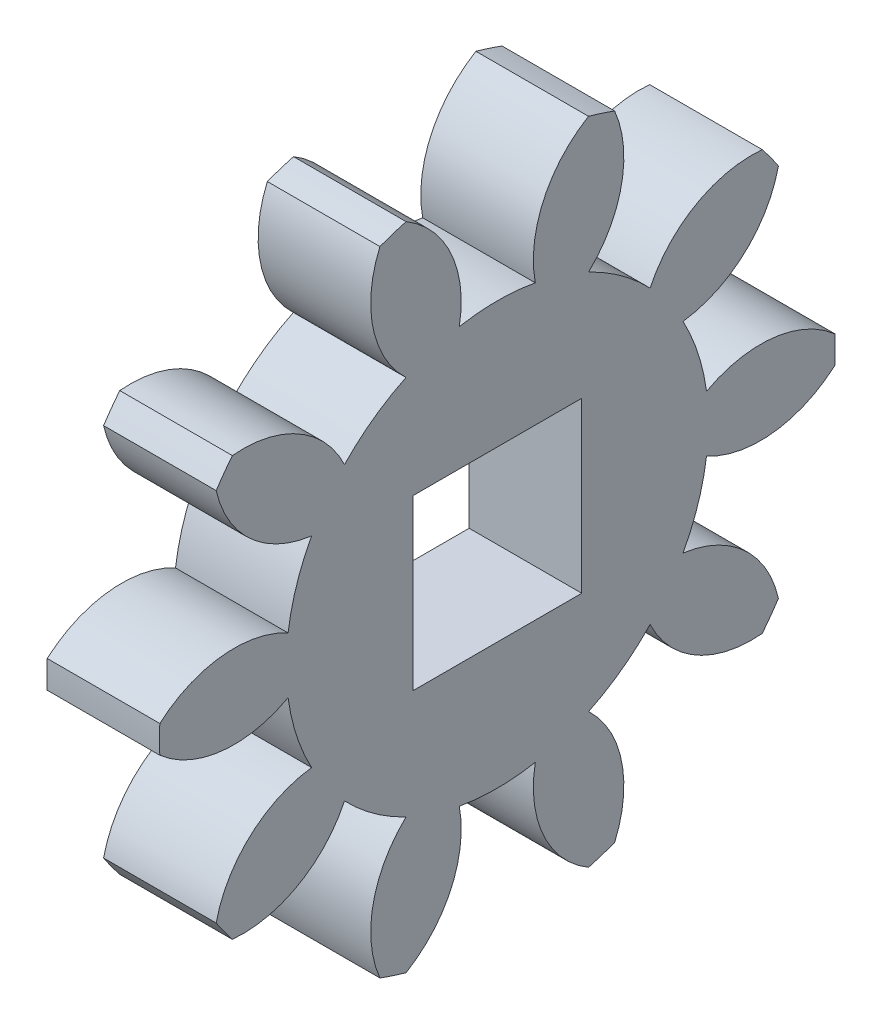
SolidWorks part; units mm, degrees
ref_plane "Plane1" through (0, 0, 0) normal (0, 0, 1) x (1, 0, 0)
ref_plane "Plane2" through (0, 0, 0) normal (0, 1, 0) x (1, 0, 0)
ref_plane "Plane3" through (0, 0, 0) normal (1, 0, 0) x (0, 0, -1)
other "Configuration Table"
sketch "HoldingSke" plane through (0, 0, 0) normal (0, 1, 0) x (1, 0, 0)
  line L0 (0, 0) -> (0.4924, -0.0868)
  line L1 (-15, 0) -> (100, 0) construction
  line L2 (0, 0) -> (-2.1039, 2.3779)
  line L3 (0, 0) -> (-11.863, 4.5341)
  line L4 (0, 0) -> (8.5048, 1.4996)
  line L5 (0, 0) -> (-46.8476, -17.4728)
  line L6 (0, 0) -> (-3.3159, -2.2372)
  line L7 (-2.1039, 2.3779) -> (8.6586, 51.2059)
  line L8 (-76.2, 54.61) -> (-75.9, 54.61)
  line L9 (-67.7845, 28.3722) -> (-49.3413, 33.142)
  line L10 (-76.2, 71.12) -> (104.1128, 71.12)
  line L11 (0, 0) -> (-4, 0)
  line L12 (-76.2, 101.6) -> (-76.133, 101.6)
  line L13 (24.9733, 27.94) -> (52.9518, 28.4284)
  line L14 (24.9733, 27.94) -> (24.9743, 27.94)
  line L15 (24.9733, 27.94) -> (100.4006, 29.5858)
  line L16 (-63.627, -2) -> (-12.827, -2)
  circle A0 centre (0, 0) radius 1
  circle A1 centre (0, 0) radius 7.499
  circle A2 centre (0, 0) radius 37.5
  circle A3 centre (0, 0) radius 1
  dimension "MHD" = 14.998
  dimension "Hub_dia" = 75
  dimension "Bore" = 2
  dimension "MBD" = 2
  dimension "Num_teeth" = 10
  dimension "Pitch" = 0.5
  dimension "Overall_len" = 50
  dimension "Show_teeth" = 10
  dimension "Thickness" = 4
  dimension "OAL" = 50.0001
  dimension "T_dim" = 0.3
  dimension "Ap" = 14.5
  dimension "H" = 19.05
  dimension "Pitch_radius" = 180.3128
  dimension "Width" = 4
  dimension "Backlash" = 0.067
  dimension "Addendum_fac" = 1
  dimension "Dedendum_fac" = 1.25
  dimension "Clearance_fac" = 0.25
  dimension "Dedendum_add" = 0.001
  dimension "Module" = 2
sketch "BasProSke" plane through (0, 0, 0) normal (0, 1, 0) x (1, 0, 0)
  line L0 (-10, 0) -> (60, 0) construction
  line L1 (0, 0) -> (0, 12)
  line L2 (0, 0) -> (4, 0)
  line L3 (4, 0) -> (4, 12)
  line L4 (4, 12) -> (0, 12)
  dimension "Thickness" = 4
  dimension "Diameter" = 24
revolve "Base-Revolve" add sketch "BasProSke" angle 360 about L0
sketch "TooCutSke" plane through (0, 0, 0) normal (1, 0, 0) x (0, 0, -1)
  line L1 (0, 0) -> (0, 107) construction
  line L2 (0, 0) -> (-1.6814, 9.8576) construction
  line L3 (0, 0) -> (-6.1153, 18.8209) construction
  line L4 (-1.6814, 9.8576) -> (-3.0576, 9.4105) construction
  arc A0 (1.35, 7.3765) -> (-1.35, 7.3765) centre (0, 0) ccw
  arc A1 (3.2708, 11.572) -> (-3.2708, 11.572) centre (0, 0) ccw
  circle A2 centre (0, 0) radius 10 construction
  circle A3 centre (0, 0) radius 9.6815 construction
  arc A4 (-1.35, 7.3765) -> (-3.2708, 11.572) centre (-5.2814, 8.1141) ccw
  arc A5 (3.2708, 11.572) -> (1.35, 7.3765) centre (5.2814, 8.1141) ccw
  dimension "Root_dia" = 14.998
  dimension "Overcut_dia" = 24.0508
  dimension "Pitch_dia" = 20
  dimension "Base_dia" = 19.363
  dimension "Flank_rad" = 4
  dimension "Half_ang" = 18
  dimension "Half_CT" = 1.4471
extrude "ToothCut" cut sketch "TooCutSke" along normal through all
fillet "Breaks" [suppressed] radius 0.04
fillet "RootFillets" [suppressed] radius 0.501
pattern_circular "TeethCuts" count 10 every 36 about axis through (-10, 0, 0) along (1, 0, 0) of "ToothCut", "RootFillets", "Breaks"
sketch "HubNeaOneSke" plane through (0, 0, 0) normal (-1, 0, 0) x (0, 0, 1)
  circle A0 centre (0, 0) radius 7.499
  dimension "Diameter" = 14.998
extrude "HubNearOne" [suppressed] add sketch "HubNeaOneSke" along normal blind 46.0001
sketch "HubNeaBotSke" plane through (0, 0, 0) normal (-1, 0, 0) x (0, 0, 1)
  circle A0 centre (0, 0) radius 7.499
  dimension "Diameter" = 14.998
extrude "HubNearBoth" [suppressed] add sketch "HubNeaBotSke" along normal blind 23
ref_plane "FarPln" through (4, 0, 0) normal (1, 0, 0) x (0, 0, -1)
sketch "HubFarSke" plane through (4, 0, 0) normal (1, 0, 0) x (0, 0, -1)
  circle A0 centre (0, 0) radius 7.499
  dimension "Diameter" = 14.998
extrude "HubFar" [suppressed] add sketch "HubFarSke" along normal blind 23
sketch "BorSke" plane through (0, 0, 0) normal (1, 0, 0) x (0, 0, -1)
  circle A0 centre (0, 0) radius 1
  dimension "Diameter" = 2
extrude "Bore" cut sketch "BorSke" along normal mid plane 100.0001
sketch "KeySke" plane through (0, 0, 0) normal (1, 0, 0) x (0, 0, -1)
  line L0 (-0.4, 0) -> (-0.4, 1.3)
  line L1 (-0.4, 1.3) -> (0.4, 1.3)
  line L2 (0.4, 1.3) -> (0.4, 0)
  line L3 (0, 0) -> (0, 34) construction
  line L4 (-0.4, 0) -> (0.4, 0)
  dimension "Offset" = 1.3
  dimension "Width" = 0.8
extrude "Keyway" [suppressed] cut sketch "KeySke" along normal mid plane 100.0001
pattern_circular "Keyway2" [suppressed] count 2 every 90 about axis through (-10, 0, 0) along (1, 0, 0)
sketch "草图1" plane through (0, 0, 0) normal (-1, 0, 0) x (0, 0, 1)
  line L1 (-3, 3) -> (3, 3)
  line L2 (-3, 3) -> (-3, -3)
  line L3 (-3, -3) -> (3, -3)
  line L4 (3, 3) -> (3, -3)
  line L5 (-3, 3) -> (3, -3) construction
  line L6 (-3, -3) -> (3, 3) construction
  point P0 (0, 0)
  dimension "D1" = 6
  dimension "D2" = 6
extrude "切除-拉伸2" cut sketch "草图1" against normal through all
equation "' \"Module@HoldingSke\" = 6.35"
equation "' \"Num_teeth@HoldingSke\" = 12"
equation "' \"Ap@HoldingSke\" =  20"
equation "' \"Ap@HoldingSke\" = 20"
equation "' \"Width@HoldingSke\" = 0.5 * 25.4"
equation "' \"Hub_dia@HoldingSke\"= 1 * 25.4"
equation "' \"Hub_dia@HoldingSke\" = 1 * 25.4"
equation "' \"Overall_len@HoldingSke\" = 1.0 * 25.4"
equation "' \"Bore@HoldingSke\" = 0.75 * 25.4"
equation "' \"T_dim@HoldingSke\" = 0.1 * 25.4"
equation "' \"Width@KeySke\" = 0.25 * 25.4"
equation "' \"Show_teeth@HoldingSke\" = 13"
equation "' \"Backlash@HoldingSke\" = 0.009 * 25.4"
equation "' \"Addendum_fac@HoldingSke\" = 1.0"
equation "' \"Dedendum_fac@HoldingSke\" = 1.25"
equation "' \"Dedendum_add@HoldingSke\" = 0.00005 * 25.4"
equation "' \"Clearance_fac@HoldingSke\" = 0.25"
equation "\"Pitch@HoldingSke\" = 1 / \"Module@HoldingSke\""
equation "\"Overcut_dia@TooCutSke\" = (\"Num_teeth@HoldingSke\" + 2 * \"Addendum_fac@HoldingSke\") / \"Pitch@HoldingSke\" + 0.002 * 25.4"
equation "\"Pitch_dia@TooCutSke\" = \"Num_teeth@HoldingSke\" / \"Pitch@HoldingSke\""
equation "\"Base_dia@TooCutSke\" = \"Num_teeth@HoldingSke\" / \"Pitch@HoldingSke\" * cos((\"Ap@HoldingSke\"  * 3.14159265 / 180))"
equation "\"Root_dia@TooCutSke\" = (\"Num_teeth@HoldingSke\" + 2) / \"Pitch@HoldingSke\" - 2 * (\"Addendum_fac@HoldingSke\" + \"Dedendum_fac@HoldingSke\") / \"Pitch@HoldingSke\" - \"Dedendum_add@HoldingSke\" * 2"
equation "\"Half_ang@TooCutSke\" = 180 / \"Num_teeth@HoldingSke\""
equation "\"Half_CT@TooCutSke\" = \"Num_teeth@HoldingSke\" / \"Pitch@HoldingSke\" * sin((3.14159265 / 2 / \"Num_teeth@HoldingSke\")) / 2 - 7 * \"Backlash@HoldingSke\" / 4"
equation "\"Flank_rad@TooCutSke\" = \"Num_teeth@HoldingSke\" / \"Pitch@HoldingSke\" / 5"
equation "\"Radius@RootFillets\" = \"Clearance_fac@HoldingSke\" / \"Pitch@HoldingSke\" + \"Dedendum_add@HoldingSke\""
equation "\"Break_rad@Breaks\" = 0.02 / \"Pitch@HoldingSke\""
equation "\"Thickness@HoldingSke\" = \"Width@HoldingSke\""
equation "\"OAL@HoldingSke\" = \"Thickness@HoldingSke\""
equation "\"MHD@HoldingSke\" = (\"Num_teeth@HoldingSke\" + 2) / \"Pitch@HoldingSke\" - 2 * (\"Addendum_fac@HoldingSke\" + \"Dedendum_fac@HoldingSke\")  / \"Pitch@HoldingSke\" - \"Dedendum_add@HoldingSke\" * 2"
equation "\"MBD@HoldingSke\" = (\"Num_teeth@HoldingSke\" + 2) / \"Pitch@HoldingSke\" - 2 * (\"Addendum_fac@HoldingSke\" + \"Dedendum_fac@HoldingSke\")  / \"Pitch@HoldingSke\" - \"Dedendum_add@HoldingSke\" * 2 - 0.002 * 25.4"
equation "\"MHD@HoldingSke\" = ((sgn( \"MHD@HoldingSke\" - \"Hub_dia@HoldingSke\" )-1)*( \"MHD@HoldingSke\" - \"Hub_dia@HoldingSke\" ))/-2+ \"Hub_dia@HoldingSke\""
equation "\"MBD@HoldingSke\" = ((sgn( \"MBD@HoldingSke\" - \"Bore@HoldingSke\" )-1)*( \"MBD@HoldingSke\" - \"Bore@HoldingSke\" ))/-2+ \"Bore@HoldingSke\""
equation "\"OAL@HoldingSke\" = ((sgn( \"OAL@HoldingSke\" - \"Overall_len@HoldingSke\" )+1)*( \"OAL@HoldingSke\" - \"Overall_len@HoldingSke\" ))/2 + \"Overall_len@HoldingSke\" + 0.000002 * 25.4"
equation "\"Num_teeth@TeethCuts\" = int( \"Show_teeth@HoldingSke\" ) + 1"
equation "\"Num_teeth@TeethCuts\" = ((sgn( \"Num_teeth@TeethCuts\" - \"Num_teeth@HoldingSke\" )-1)*( \"Num_teeth@TeethCuts\" - \"Num_teeth@HoldingSke\" ))/-2+ \"Num_teeth@HoldingSke\""
equation "\"Num_teeth@TeethCuts\" = ((sgn( \"Num_teeth@TeethCuts\" - 2.0)+1)*( \"Num_teeth@TeethCuts\" - 2.0))/2 +2.0"
equation "\"Angle@TeethCuts\" = 360.0 / \"Num_teeth@HoldingSke\""
equation "\"Diameter@BasProSke\" = (\"Num_teeth@HoldingSke\" + 2 * \"Addendum_fac@HoldingSke\") / \"Pitch@HoldingSke\""
equation "\"Thickness@BasProSke\"  = \"Thickness@HoldingSke\""
equation "' \"Fillet_rad@BasProSke\" =  \"Thickness@HoldingSke\" * 0.05"
equation "' \"Fillet_rad@BasProSke\" = \"Thickness@HoldingSke\" * 0.05"
equation "\"MHD@HoldingSke\" = ((sgn( \"MHD@HoldingSke\" - \"Root_dia@TooCutSke\" )-1)*( \"MHD@HoldingSke\" - \"Root_dia@TooCutSke\" ))/-2+ \"Root_dia@TooCutSke\""
equation "\"Diameter@HubNeaOneSke\" = \"MHD@HoldingSke\""
equation "\"Length@HubNearOne\" = \"OAL@HoldingSke\" - \"Thickness@BasProSke\""
equation "\"Diameter@HubNeaBotSke\" = \"MHD@HoldingSke\""
equation "\"Length@HubNearBoth\" = ( \"OAL@HoldingSke\" - \"Thickness@BasProSke\" ) / 2.0"
equation "\"Thickness@FarPln\" = \"Thickness@BasProSke\""
equation "\"Diameter@HubFarSke\" = \"MHD@HoldingSke\""
equation "\"Length@HubFar\" = ( \"OAL@HoldingSke\" - \"Thickness@BasProSke\" ) / 2.0"
equation "\"Diameter@BorSke\" = \"MBD@HoldingSke\""
equation "\"D1@Bore\" = \"OAL@HoldingSke\" * 2.0"
equation "\"D1@Keyway\" = \"OAL@HoldingSke\" * 2.0"
equation "\"Offset@KeySke\" = \"T_dim@HoldingSke\" + \"MBD@HoldingSke\" / 2.0"
